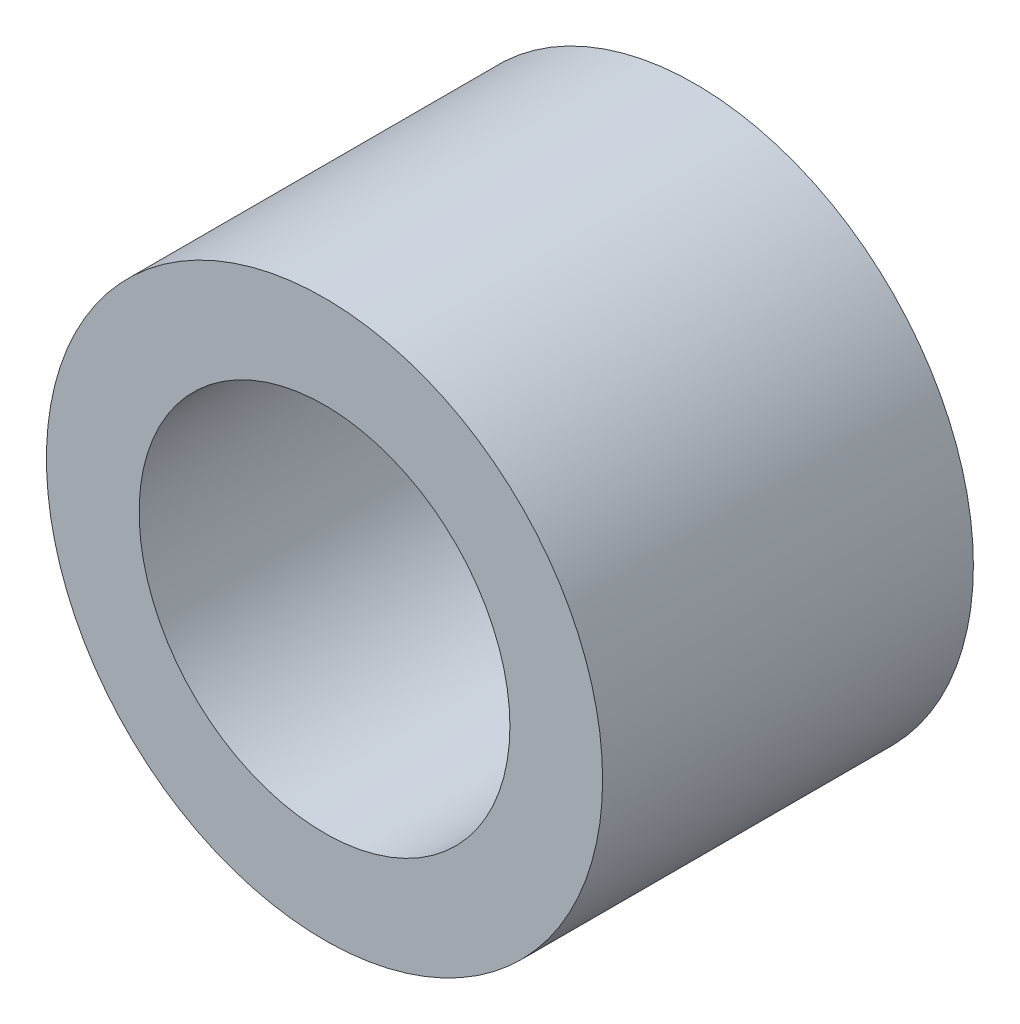
SolidWorks part; units mm, degrees
ref_plane "Front Plane" through (0, 0, 0) normal (0, 0, 1) x (1, 0, 0)
ref_plane "Top Plane" through (0, 0, 0) normal (0, 1, 0) x (1, 0, 0)
ref_plane "Right Plane" through (0, 0, 0) normal (1, 0, 0) x (0, 0, -1)
sketch "Sketch1" plane through (0, 0, 0) normal (0, 0, 1) x (1, 0, 0)
  circle A0 centre (0, 0) radius 3
  circle A1 centre (0, 0) radius 2
  dimension "D1" = 4
  dimension "D2" = 6
extrude "Boss-Extrude1" add sketch "Sketch1" along normal blind 4
